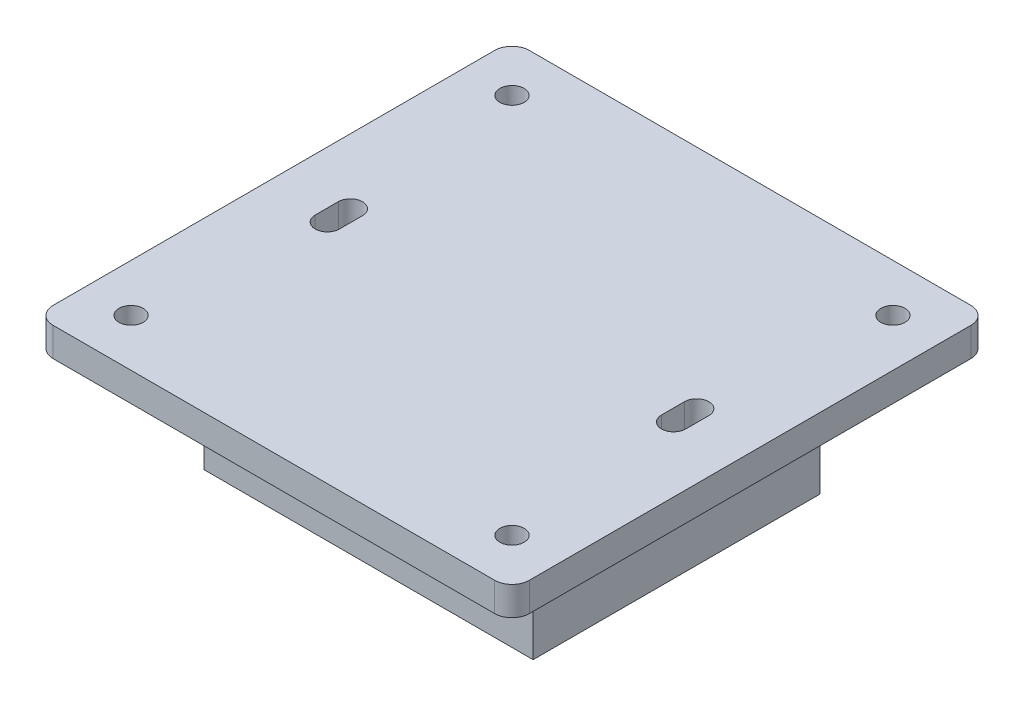
SolidWorks part; units mm, degrees
ref_plane "Спереди" through (0, 0, 0) normal (0, 0, 1) x (1, 0, 0)
ref_plane "Сверху" through (0, 0, 0) normal (0, 1, 0) x (1, 0, 0)
ref_plane "Справа" through (0, 0, 0) normal (1, 0, 0) x (0, 0, -1)
sketch "Эскиз1" plane through (0, 0, 0) normal (0, 1, 0) x (1, 0, 0)
  line L0 (-45.3101, 0) -> (44.913, 0) construction
  line L5 (-41.3789, 41.3789) -> (41.3789, -41.3789) construction
  line L6 (-39.2479, -39.2479) -> (43.51, 43.51) construction
  line L7 (-38.25, -41.25) -> (38.25, -41.25)
  line L8 (-41.25, -38.25) -> (-41.25, 38.25)
  line L9 (-38.25, 41.25) -> (38.25, 41.25)
  line L10 (41.25, -38.25) -> (41.25, 38.25)
  line L11 (-41.25, -41.25) -> (41.25, 41.25) construction
  line L12 (-41.25, 41.25) -> (41.25, -41.25) construction
  line L13 (0, 44.7945) -> (0, -43.8485) construction
  line L14 (-32.1, 2) -> (-32.1, -2)
  line L15 (-27.9, -2) -> (-27.9, 2)
  line L16 (32.1, -2) -> (32.1, 2)
  line L17 (27.9, -2) -> (27.9, 2)
  circle A4 centre (-33, 33) radius 2.1
  circle A5 centre (33, 33) radius 2.1
  circle A6 centre (33, -33) radius 2.1
  circle A7 centre (-33, -33) radius 2.1
  arc A8 (-38.25, -41.25) -> (-41.25, -38.25) centre (-38.25, -38.25) cw
  arc A9 (-41.25, 38.25) -> (-38.25, 41.25) centre (-38.25, 38.25) cw
  arc A10 (38.25, 41.25) -> (41.25, 38.25) centre (38.25, 38.25) cw
  arc A11 (38.25, -41.25) -> (41.25, -38.25) centre (38.25, -38.25) ccw
  arc A12 (-32.1, 2) -> (-27.9, 2) centre (-30, 2) cw
  arc A13 (-32.1, -2) -> (-27.9, -2) centre (-30, -2) ccw
  arc A14 (32.1, -2) -> (27.9, -2) centre (30, -2) cw
  arc A15 (32.1, 2) -> (27.9, 2) centre (30, 2) ccw
  point P0 (0, 0)
  point P6 (0, 0)
  dimension "D1" = 3
  dimension "D2" = 4
extrude "Бобышка-Вытянуть1" add sketch "Эскиз1" along normal blind 5
sketch "Эскиз2" plane through (0, 0, 0) normal (0, -1, 0) x (1, 0, 0)
  line L5 (-28.5, 24.8387) -> (28.5, 24.8387)
  line L6 (-28.5, 24.8387) -> (-28.5, -24.8387)
  line L7 (-28.5, -24.8387) -> (28.5, -24.8387)
  line L8 (28.5, 24.8387) -> (28.5, -24.8387)
  line L9 (-28.5, 24.8387) -> (28.5, -24.8387) construction
  line L10 (-28.5, -24.8387) -> (28.5, 24.8387) construction
  point P0 (0, 0)
extrude "Бобышка-Вытянуть2" add sketch "Эскиз2" along normal blind 20
